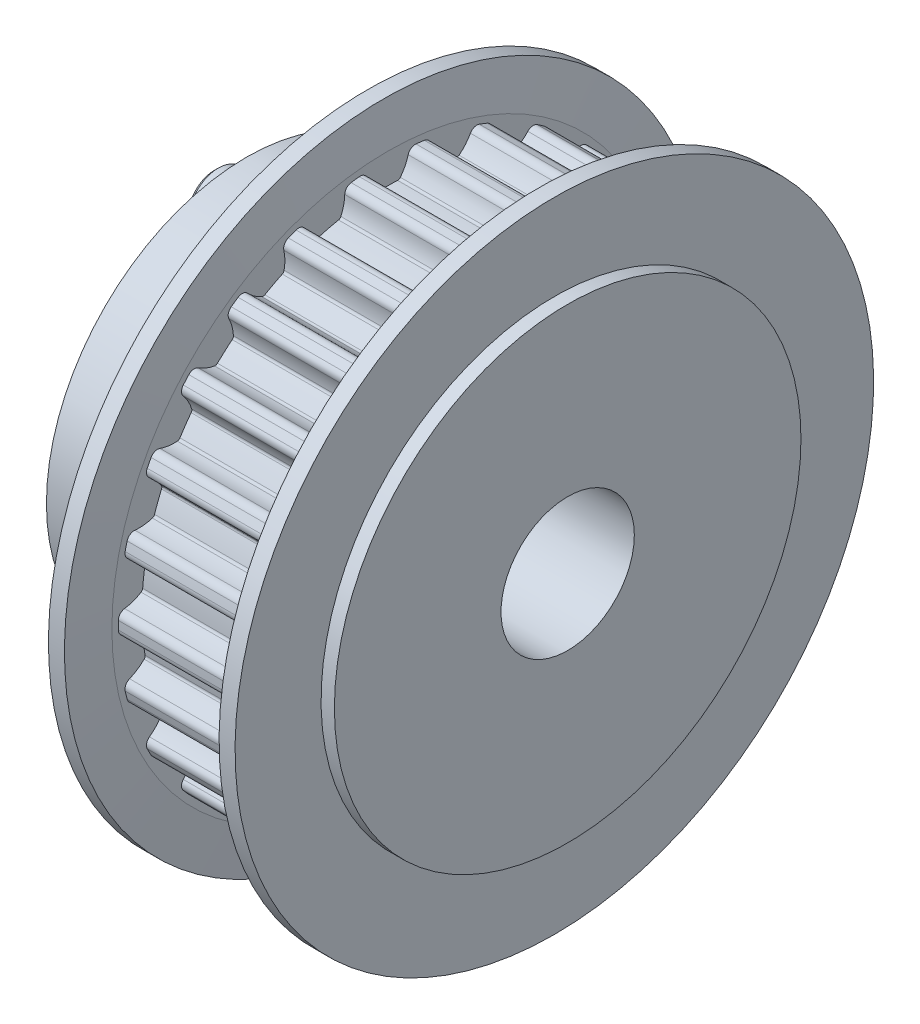
SolidWorks part; units mm, degrees
ref_plane "前视基准面" through (0, 0, 0) normal (0, 0, 1) x (1, 0, 0)
ref_plane "上视基准面" through (0, 0, 0) normal (0, 1, 0) x (1, 0, 0)
ref_plane "右视基准面" through (0, 0, 0) normal (1, 0, 0) x (0, 0, -1)
sketch "草图1" plane through (0, 0, 0) normal (0, 0, 1) x (1, 0, 0)
  line L0 (-8, 0) -> (-8, 17.5)
  line L1 (-8, 17.5) -> (-5.5, 17.5)
  line L2 (-5.5, 17.5) -> (-5.5, 20.21)
  line L3 (-5.5, 20.21) -> (5.5, 20.21)
  line L4 (5.5, 20.21) -> (5.5, 17.5)
  line L5 (5.5, 17.5) -> (8, 17.5)
  line L6 (8, 17.5) -> (8, 0)
  line L7 (8, 0) -> (-8, 0)
  dimension "D1" = 11
  dimension "D2" = 16
  dimension "D3" = 17.5
  dimension "D4" = 20.21
revolve "旋转1" add sketch "草图1" angle 360 about L7
sketch "草图2" plane through (-5.5, 0, 0) normal (-1, 0, 0) x (0, 0, 1)
  line L0 (0, 0) -> (0, 20.21) construction
  arc A0 (0.8638, 18.4198) -> (-0.8638, 18.4198) centre (0, 0) ccw
  arc A1 (1.625, 20.1446) -> (-1.625, 20.1446) centre (0, 0) ccw
  circle A2 centre (0, 0) radius 20.21 construction
  arc A3 (-0.8638, 18.4198) -> (-1.625, 20.1446) centre (1.625, 20.5485) cw
  arc A4 (0.8638, 18.4198) -> (1.625, 20.1446) centre (-1.625, 20.5485) ccw
  dimension "D1" = 3.25
  dimension "D2" = 1.77
  dimension "D3" = 3.275
extrude "切除-拉伸1" cut sketch "草图2" against normal through all
fillet "圆角1" radius 0.55 2 edges at (0, 20.1446, 1.625) (0, 20.1446, -1.625)
fillet "圆角2" radius 0.25 2 edges at (0, 18.4198, 0.8638) (0, 18.4198, -0.8638)
pattern_circular "阵列(圆周)1" count 26 over 360 about axis through (0, 0, 0) along (1, 0, 0) of "切除-拉伸1", "圆角2", "圆角1"
sketch "草图3" plane through (0, 0, 0) normal (0, 0, 1) x (1, 0, 0)
  line L0 (-7, 17.5) -> (-7, 23.95)
  line L1 (-7, 23.95) -> (-5.8, 23.95)
  line L2 (-5.8, 23.95) -> (-5.5, 20.69)
  line L3 (-5.5, 20.69) -> (-5.5, 17.5)
  line L4 (-5.5, 17.5) -> (-8, 17.5) construction
  line L5 (-5.5, 17.5) -> (-7, 17.5)
  line L6 (0, -1000) -> (0, 49000) construction
  line L8 (5.5, 20.69) -> (5.5, 17.5)
  line L9 (5.8, 23.95) -> (5.5, 20.69)
  line L10 (5.5, 17.5) -> (7, 17.5)
  line L11 (7, 17.5) -> (7, 23.95)
  line L12 (7, 23.95) -> (5.8, 23.95)
  line L13 (-8, 0) -> (8, 0) construction
  line L14 (-8, 17.5) -> (-8, -17.5) construction
  line L15 (8, -17.5) -> (8, 17.5) construction
  dimension "D1" = 5.5
  dimension "D2" = 1.5
  dimension "D3" = 17.5
  dimension "D4" = 23.95
  dimension "D5" = 20.69
  dimension "D6" = 1.2
revolve "旋转2" add sketch "草图3" angle 360 about L13
sketch "草图4" plane through (0, 0, 0) normal (0, 0, 1) x (1, 0, 0)
  line L0 (-8, 17.5) -> (-8, -17.5) construction
  line L1 (-8, 0) -> (-1.6, 0)
  line L2 (-8, 0) -> (-8, 15)
  line L3 (-8, 15) -> (-1.6, 15)
  line L4 (-1.6, 0) -> (-1.6, 15)
  dimension "D1" = 6.4
  dimension "D2" = 15
revolve "切除-旋转1" [suppressed] cut sketch "草图4" angle 360 about L1
sketch "草图5" plane through (0, 0, 0) normal (0, 0, 1) x (1, 0, 0)
  line L0 (-9.8, 14.5) -> (-8.4, 14.5)
  line L1 (-8.1, 14.2) -> (-8.1, 7)
  line L2 (-0.6, 0) -> (-10.1, 0)
  line L3 (-10.1, 0) -> (-10.1, 14.2)
  line L4 (-7, 23.95) -> (-7, -23.95) construction
  line L5 (-8.1, 7) -> (-0.6, 7)
  line L6 (-0.6, 7) -> (-0.6, 0)
  arc A0 (-8.1, 14.2) -> (-8.4, 14.5) centre (-8.4, 14.2) ccw
  arc A1 (-9.8, 14.5) -> (-10.1, 14.2) centre (-9.8, 14.2) ccw
  point P9 (-8.1, 14.5)
  point P12 (-10.1, 14.5)
  dimension "D5" = 0.3
  dimension "D1" = 14.5
  dimension "D2" = 2
  dimension "D3" = 7.5
  dimension "D4" = 7
  dimension "D6" = 6.4
revolve "旋转3" [suppressed] add sketch "草图5" angle 360 about L2
sketch "草图6" [suppressed] plane through (-3.6, 0, 0) normal (-1, 0, 0) x (0, 0, 1)
  circle A0 centre (0, 10.5) radius 2.25
  dimension "D1" = 4.5
  dimension "D2" = 10.5
extrude "凸台-拉伸1" [suppressed] add sketch "草图6" along normal blind 2.4
fillet "圆角3" [suppressed] radius 0.3
sketch "草图7" [suppressed] plane through (-6, 0, 0) normal (-1, 0, 0) x (0, 0, 1)
  line L1 (0, 11.9896) -> (-1.29, 11.2448)
  line L2 (-1.29, 11.2448) -> (-1.29, 9.7552)
  line L3 (-1.29, 9.7552) -> (0, 9.0104)
  line L4 (0, 9.0104) -> (1.29, 9.7552)
  line L5 (1.29, 9.7552) -> (1.29, 11.2448)
  line L6 (1.29, 11.2448) -> (0, 11.9896)
  circle A0 centre (0, 10.5) radius 1.29 construction
  dimension "D1" = 2.58
extrude "切除-拉伸2" [suppressed] cut sketch "草图7" against normal blind 0.9
pattern_circular "阵列(圆周)2" [suppressed] count 3 over 360
sketch "草图8" [suppressed] plane through (-3.6, 0, 0) normal (-1, 0, 0) x (0, 0, 1)
  line L0 (0, 0) -> (9.0933, 5.25) construction
  line L1 (0, 23.95) -> (0, -23.95) construction
  circle A0 centre (9.0933, 5.25) radius 1.29
  circle A1 centre (0, 0) radius 23.95 construction
  dimension "D2" = 2.58
  dimension "D1" = 60
  dimension "D3" = 10.5
extrude "切除-拉伸3" [suppressed] cut sketch "草图8" against normal blind 2
cosmetic thread "装饰螺纹线1" [suppressed] parameters "D2"=3
pattern_circular "阵列(圆周)3" [suppressed] count 3 over 360
sketch "草图9" plane through (8, 0, 0) normal (1, 0, 0) x (0, 0, -1)
  circle A0 centre (0, 10.5) radius 1.29
  dimension "D1" = 2.58
  dimension "D2" = 10.5
extrude "切除-拉伸4" [suppressed] cut sketch "草图9" against normal blind 6
cosmetic thread "装饰螺纹线2" [suppressed] parameters "D2"=3
pattern_circular "阵列(圆周)4" [suppressed] count 3 over 360
sketch "草图11" plane through (0, 0, 0) normal (0, 0, 1) x (1, 0, 0)
  line L0 (-8, 5.5) -> (-10, 5.5)
  line L2 (-10, 5.5) -> (-10, 15)
  line L3 (-10, 15) -> (-16.1, 15)
  line L4 (-16.1, 15) -> (-16.1, 0)
  line L5 (-16.1, 0) -> (-8, 0)
  line L6 (-8, 0) -> (-8, 5.5)
  line L9 (-8, 17.5) -> (-8, -17.5) construction
  dimension "D1" = 15
  dimension "D2" = 5.5
  dimension "D3" = 8.1
  dimension "D4" = 2
revolve "旋转4" add sketch "草图11" angle 360 about L5
sketch "草图12" plane through (0, 0, 0) normal (0, 0, 1) x (1, 0, 0)
  line L0 (-18.2, 13.25) -> (-16.1, 13.25)
  line L1 (-16.1, 15) -> (-16.1, -15) construction
  line L2 (-16.1, 13.25) -> (-16.1, 12.5)
  line L3 (-16.1, 12.5) -> (-7, 12.5)
  line L5 (-7, 12.5) -> (-7, 11)
  line L6 (-7, 11) -> (-18.5, 11)
  line L7 (-18.5, 11) -> (-18.5, 12.95)
  line L8 (-18.5, 12.95) -> (-18.2, 13.25)
  line L9 (-7, 23.95) -> (-7, -23.95) construction
  point P0 (-18.5, 13.25)
  dimension "D1" = 11
  dimension "D2" = 2.4
  dimension "D3" = 1.5
  dimension "D4" = 2.25
  dimension "D5" = 0.3
  dimension "D6" = 45
revolve "旋转5" add sketch "草图12" angle 360 about L6
sketch "草图13" plane through (-18.5, 0, 0) normal (-1, 0, 0) x (0, 0, 1)
  line L1 (0, 12.4896) -> (-1.29, 11.7448)
  line L2 (-1.29, 11.7448) -> (-1.29, 10.2552)
  line L3 (-1.29, 10.2552) -> (0, 9.5104)
  line L4 (0, 9.5104) -> (1.29, 10.2552)
  line L5 (1.29, 10.2552) -> (1.29, 11.7448)
  line L6 (1.29, 11.7448) -> (0, 12.4896)
  circle A0 centre (0, 11) radius 1.29 construction
  dimension "D1" = 2.58
extrude "切除-拉伸5" cut sketch "草图13" against normal blind 0.9
pattern_circular "阵列(圆周)5" count 3 over 360 about axis through (0, 0, 0) along (1, 0, 0) of "旋转5", "切除-拉伸5"
sketch "草图14" plane through (-16.1, 0, 0) normal (-1, 0, 0) x (0, 0, 1)
  line L0 (0, 0) -> (9.5263, 5.5) construction
  line L1 (0, -23.95) -> (0, 23.95) construction
  circle A0 centre (9.5263, 5.5) radius 1.29
  circle A1 centre (0, 0) radius 23.95 construction
  dimension "D1" = 2.58
  dimension "D2" = 11
  dimension "D3" = 60
extrude "切除-拉伸6" cut sketch "草图14" against normal up to next (6.1 mm away)
cosmetic thread "装饰螺纹线3" parameters "D2"=3
pattern_circular "阵列(圆周)6" count 3 over 360 about axis through (0, 0, 0) along (1, 0, 0) of "切除-拉伸6"
sketch "草图15" plane through (8, 0, 0) normal (1, 0, 0) x (0, 0, -1)
  circle A0 centre (0, 0) radius 5
  dimension "D1" = 10
extrude "切除-拉伸7" cut sketch "草图15" against normal through all
